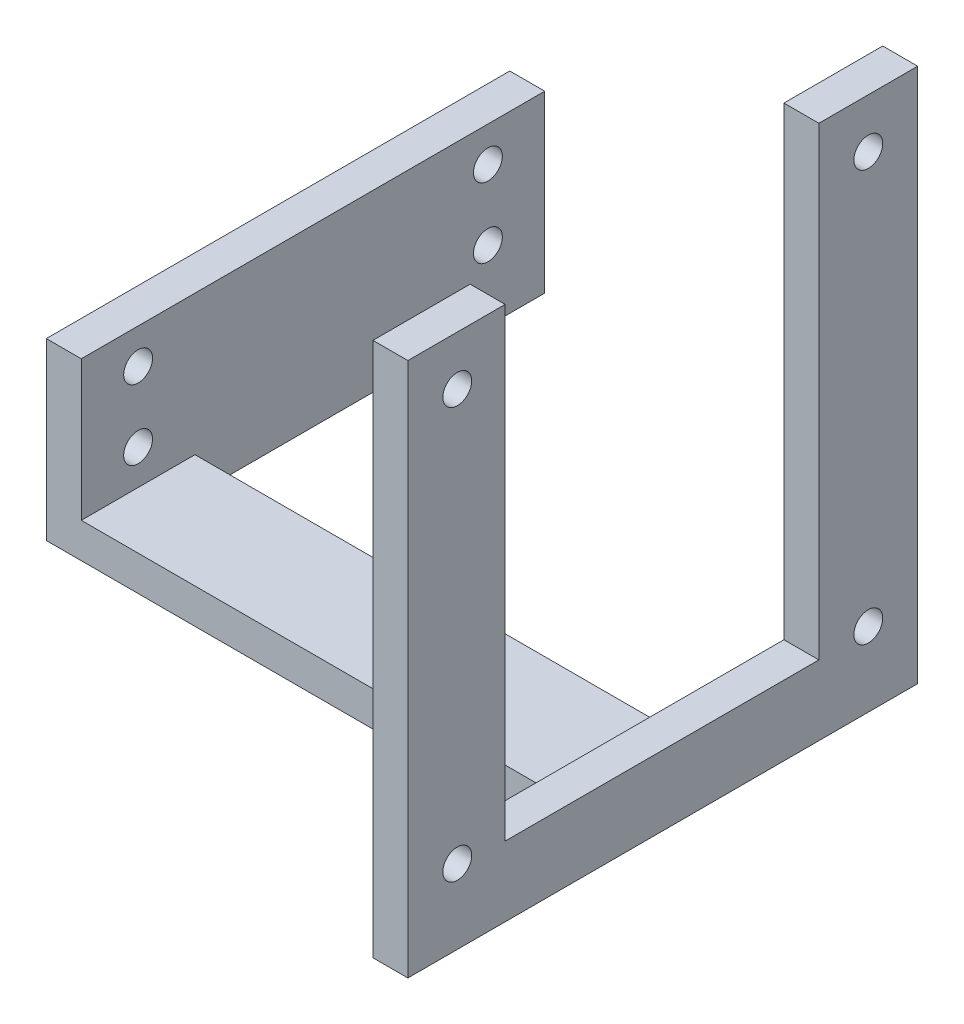
SolidWorks part; units mm, degrees
ref_plane "Front Plane" through (0, 0, 0) normal (0, 0, 1) x (1, 0, 0)
ref_plane "Top Plane" through (0, 0, 0) normal (0, 1, 0) x (1, 0, 0)
ref_plane "Right Plane" through (0, 0, 0) normal (1, 0, 0) x (0, 0, -1)
sketch "Sketch1" plane through (0, 0, 0) normal (1, 0, 0) x (0, 0, -1)
  line L1 (0, 0) -> (13, 0)
  line L2 (0, 0) -> (0, -16)
  line L3 (0, -16) -> (13, -16)
  line L4 (13, 0) -> (13, -16)
  dimension "D1" = 13
  dimension "D2" = 16
extrude "Boss-Extrude1" add sketch "Sketch1" along normal blind 4
sketch "Sketch2" plane through (4, 0, 0) normal (1, 0, 0) x (0, 0, -1)
  line L0 (13, 0) -> (0, 0) construction
  line L1 (0, -16) -> (13, -16) construction
  line L2 (13, -16) -> (13, 0) construction
  line L3 (0, 0) -> (0, -16) construction
  circle A0 centre (6.5, -4) radius 1.65
  circle A1 centre (6.5, -12) radius 1.65
  dimension "D1" = 3.3
  dimension "D2" = 3.3
  dimension "D3" = 4
  dimension "D4" = 4
  dimension "D5" = 6.5
  dimension "D6" = 6.5
extrude "Cut-Extrude1" cut sketch "Sketch2" against normal blind 10
sketch "Sketch3" plane through (0, -16, 0) normal (0, -1, 0) x (1, 0, 0)
  line L1 (4, 0) -> (0, 0)
  line L2 (4, 0) -> (4, -13)
  line L3 (4, -13) -> (0, -13)
  line L4 (0, 0) -> (0, -13)
extrude "Boss-Extrude2" add sketch "Sketch3" along normal blind 4
sketch "Sketch4" plane through (4, 0, 0) normal (1, 0, 0) x (0, 0, -1)
  line L0 (13, -20) -> (13, 0) construction
  line L1 (0, -20) -> (13, -20)
  line L2 (0, -20) -> (0, -16)
  line L3 (0, -16) -> (13, -16)
  line L4 (13, -20) -> (13, -16)
  dimension "D1" = 4
extrude "Boss-Extrude3" add sketch "Sketch4" along normal blind 60
sketch "Sketch6" plane through (0, -16, 0) normal (0, 1, 0) x (1, 0, 0)
  line L0 (64, 0) -> (4, 0) construction
  line L1 (64, 13) -> (60, 13)
  line L2 (64, 13) -> (64, -21)
  line L3 (64, -21) -> (60, -21)
  line L4 (60, 13) -> (60, -21)
  line L7 (64, 13) -> (60, 13)
  line L8 (64, 13) -> (64, 34)
  line L9 (64, 34) -> (60, 34)
  line L10 (60, 13) -> (60, 34)
  line M2 (4, 0) -> (64, 0)
  line M3 (64, 0) -> (64, 13)
  line M4 (64, 13) -> (4, 13)
  dimension "D1" = 4
  dimension "D2" = 21
  dimension "D3" = 21
extrude "Boss-Extrude4" add sketch "Sketch6" along normal blind 28 contours L4 L3 L2 M2 | L10 L8 L9 M4 | L4 M4 M2 M3
sketch "Sketch12" plane through (0, 0, -34) normal (0, 0, -1) x (-1, 0, 0)
  line L1 (-60, -16) -> (-64, -16)
  line L2 (-60, -16) -> (-60, 12)
  line L3 (-60, 12) -> (-64, 12)
  line L4 (-64, -16) -> (-64, 12)
extrude "Boss-Extrude8" add sketch "Sketch12" along normal blind 1.65
sketch "Sketch13" plane through (0, 0, 21) normal (0, 0, 1) x (1, 0, 0)
  line L1 (60, 12) -> (64, 12)
  line L2 (60, 12) -> (60, -16)
  line L3 (60, -16) -> (64, -16)
  line L4 (64, 12) -> (64, -16)
extrude "Boss-Extrude9" add sketch "Sketch13" along normal blind 1.65
sketch "Sketch14" plane through (0, 12, 0) normal (0, 1, 0) x (1, 0, 0)
  line L0 (64, 35.65) -> (64, -22.65) construction
  line L1 (64, 24.35) -> (60, 24.35)
  line L2 (64, 24.35) -> (64, -11.5284)
  line L3 (64, -11.5284) -> (60, -11.5284)
  line L4 (60, 24.35) -> (60, -11.5284)
  line L5 (60, 35.65) -> (60, -22.65) construction
  line L6 (64, -22.65) -> (60, -22.65) construction
  line L7 (60, 35.65) -> (64, 35.65) construction
  point P10 (62, -22.65)
  dimension "D1" = 11.3
  dimension "D2" = 11.3
extrude "Cut-Extrude5" cut sketch "Sketch14" against normal blind 24
sketch "Sketch15" plane through (64, 0, 0) normal (1, 0, 0) x (0, 0, -1)
  line L0 (-11.5284, 12) -> (-22.65, 12) construction
  line L1 (35.65, 12) -> (24.35, 12) construction
  line L2 (-22.65, -16) -> (-22.65, 12) construction
  line L3 (35.65, 12) -> (35.65, -16) construction
  circle A0 centre (-17, -11.5) radius 1.65
  circle A1 centre (30, -11.5) radius 1.65
  dimension "D1" = 3.3
  dimension "D2" = 3.3
  dimension "D3" = 23.5
  dimension "D4" = 23.5
  dimension "D5" = 5.65
  dimension "D6" = 5.65
extrude "Cut-Extrude6" cut sketch "Sketch15" against normal blind 24
sketch "Sketch16" plane through (0, 12, 0) normal (0, 1, 0) x (1, 0, 0)
  line L1 (60, -22.65) -> (64, -22.65)
  line L2 (60, -22.65) -> (60, -11.5284)
  line L3 (60, -11.5284) -> (64, -11.5284)
  line L4 (64, -22.65) -> (64, -11.5284)
  line L5 (60, 24.35) -> (64, 24.35)
  line L6 (60, 24.35) -> (60, 35.65)
  line L7 (60, 35.65) -> (64, 35.65)
  line L8 (64, 24.35) -> (64, 35.65)
extrude "Boss-Extrude10" add sketch "Sketch16" along normal blind 29.15
sketch "Sketch17" plane through (64, 0, 0) normal (1, 0, 0) x (0, 0, -1)
  line L0 (-22.65, -16) -> (-22.65, 41.15) construction
  line L1 (35.65, 41.15) -> (35.65, -16) construction
  line L2 (-22.65, 41.15) -> (-11.5284, 41.15) construction
  line L3 (24.35, 41.15) -> (35.65, 41.15) construction
  circle A0 centre (-17, 35.5) radius 1.65
  circle A1 centre (30, 35.5) radius 1.65
  point P4 (0, 0)
  dimension "D1" = 3.3
  dimension "D2" = 3.3
  dimension "D4" = 5.65
  dimension "D3" = 5.65
  dimension "D5" = 5.65
  dimension "D6" = 5.65
extrude "Cut-Extrude8" cut sketch "Sketch17" against normal blind 29.15
sketch "Sketch18" plane through (64, 0, 0) normal (1, 0, 0) x (0, 0, -1)
  line L1 (-22.65, -16) -> (13, -16)
  line L2 (-22.65, -16) -> (-22.65, -20)
  line L3 (-22.65, -20) -> (13, -20)
  line L4 (13, -16) -> (13, -20)
  line L5 (0, -20) -> (35.65, -20)
  line L6 (0, -20) -> (0, -16)
  line L7 (0, -16) -> (35.65, -16)
  line L8 (35.65, -20) -> (35.65, -16)
  line M9 (-22.65, -16) -> (0, -16)
  line M10 (0, -16) -> (0, -20)
  line M11 (0, -20) -> (13, -20)
  line M12 (13, -20) -> (13, -16)
  line M13 (13, -16) -> (35.65, -16)
extrude "Boss-Extrude11" add sketch "Sketch18" against normal blind 4 contours L2 L3 M10 M9 | L5 L8 M13 M12 | L1 M10 M11 M12
sketch "Sketch19" plane through (0, 0, -13) normal (0, 0, -1) x (-1, 0, 0)
  line L1 (0, -20) -> (-4, -20)
  line L2 (0, -20) -> (0, 0)
  line L3 (0, 0) -> (-4, 0)
  line L4 (-4, -20) -> (-4, 0)
extrude "Boss-Extrude12" add sketch "Sketch19" along normal blind 40
sketch "Sketch20" plane through (0, 0, 0) normal (-1, 0, 0) x (0, 0, 1)
  line L0 (-53, 0) -> (0, 0) construction
  line L1 (-53, -20) -> (-53, 0) construction
  circle A0 centre (-46.5, -4) radius 1.65
  circle A1 centre (-46.5, -12) radius 1.65
  point P4 (0, 0)
  dimension "D1" = 3.3
  dimension "D2" = 3.3
  dimension "D3" = 4
  dimension "D4" = 8
  dimension "D5" = 6.5
  dimension "D6" = 6.5
extrude "Cut-Extrude9" cut sketch "Sketch20" against normal blind 40
